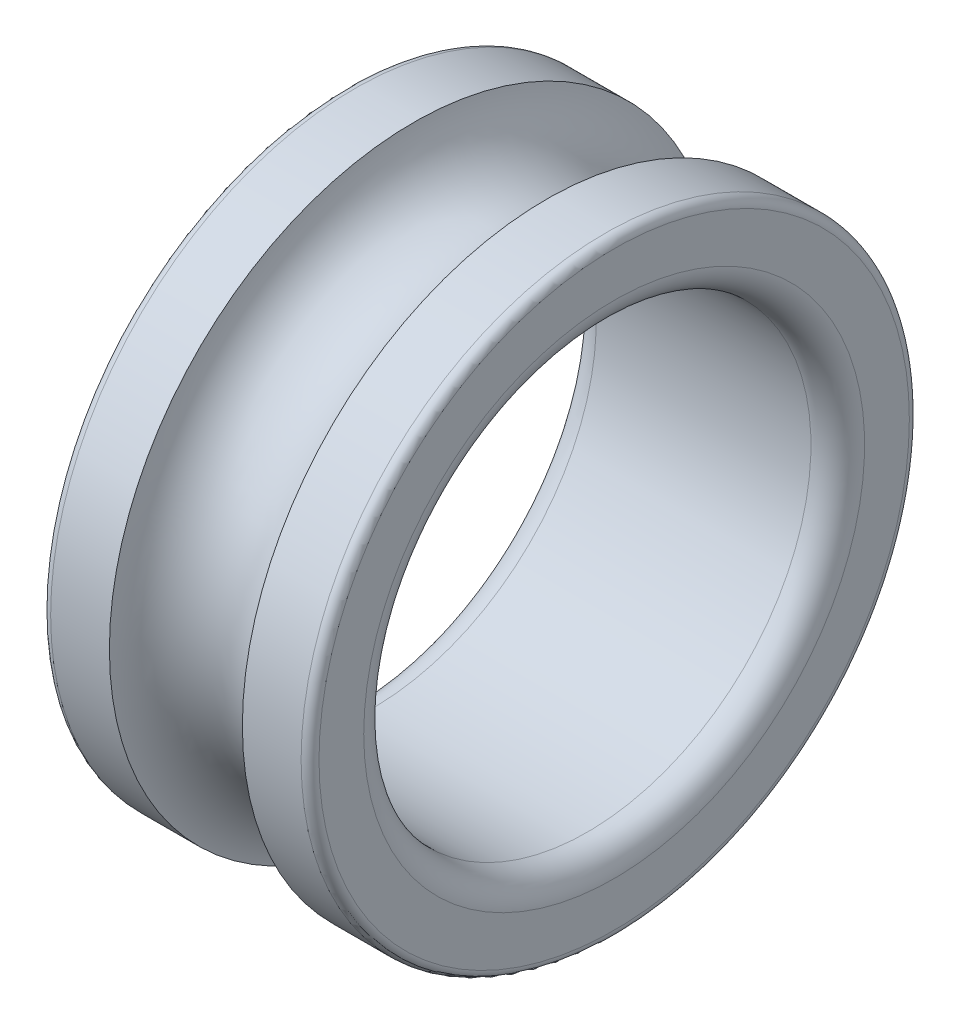
SolidWorks part; units mm, degrees
ref_plane "Front Plane" through (0, 0, 0) normal (0, 0, 1) x (1, 0, 0)
ref_plane "Top Plane" through (0, 0, 0) normal (0, 1, 0) x (1, 0, 0)
ref_plane "Right Plane" through (0, 0, 0) normal (1, 0, 0) x (0, 0, -1)
ref_plane "Plane1" through (0, 0, 0) normal (0, 0, -1) x (-1, 0, 0)
sketch "Sketch1" plane through (0, 0, 0) normal (0, 0, -1) x (-1, 0, 0)
  line L0 (-2.35, 3.4) -> (-3.0067, 3.4)
  line L1 (-4.4933, 3.4) -> (-5.15, 3.4)
  line L2 (-5.25, 3.3) -> (-5.25, 2.8)
  line L3 (-4.95, 2.5) -> (-2.55, 2.5)
  line L4 (-2.25, 2.8) -> (-2.25, 3.3)
  line L5 (-7.0013, 0) -> (0.0013, 0) construction
  line L6 (-15.6375, 0) -> (14.6064, 0) construction
  line L7 (-3.75, 3.5) -> (-3.75, -5.115) construction
  arc A0 (-3.0067, 3.4) -> (-4.4933, 3.4) centre (-3.75, 3.5) cw
  arc A1 (-5.15, 3.4) -> (-5.25, 3.3) centre (-5.15, 3.3) ccw
  arc A2 (-5.25, 2.8) -> (-4.95, 2.5) centre (-4.95, 2.8) ccw
  arc A3 (-2.55, 2.5) -> (-2.25, 2.8) centre (-2.55, 2.8) ccw
  arc A4 (-2.25, 3.3) -> (-2.35, 3.4) centre (-2.35, 3.3) ccw
  dimension "D2" = 0.3
  dimension "D3" = 0.75
  dimension "D1" = 5
  dimension "D4" = 6.8
  dimension "D5" = 7
  dimension "D6" = 3
revolve "Revolve1" add sketch "Sketch1" angle 360 about L5
